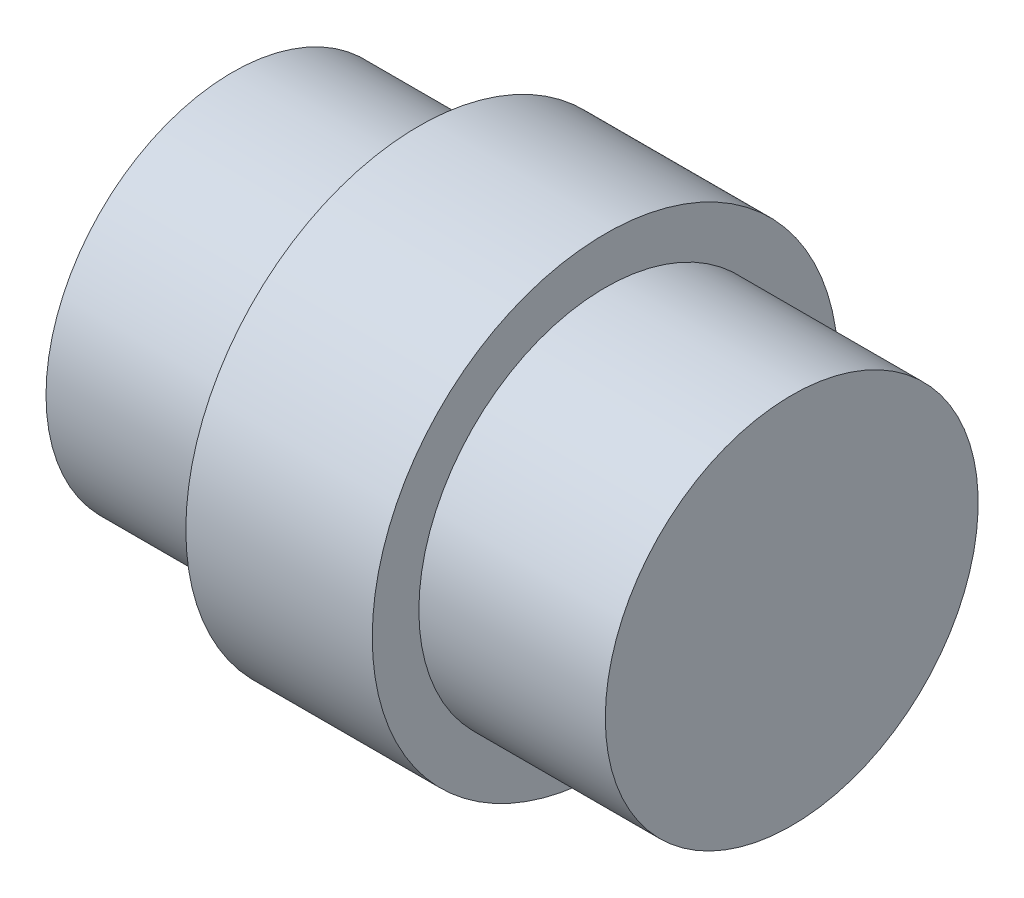
SolidWorks part; units mm, degrees
material "Plain Carbon Steel"
ref_plane "Front Plane" through (0, 0, 0) normal (0, 0, 1) x (1, 0, 0)
ref_plane "Top Plane" through (0, 0, 0) normal (0, 1, 0) x (1, 0, 0)
ref_plane "Right Plane" through (0, 0, 0) normal (1, 0, 0) x (0, 0, -1)
sketch "Sketch1" plane through (0, 0, 0) normal (1, 0, 0) x (0, 0, -1)
  circle A0 centre (0, 0) radius 12.5
  dimension "D1" = 25
extrude "Boss-Extrude1" add sketch "Sketch1" along normal mid plane 30
sketch "Sketch2" plane through (-15, 0, 0) normal (-1, 0, 0) x (0, 0, 1)
  circle A0 centre (0, 0) radius 10
  circle A1 centre (0, 0) radius 12.5
  dimension "D1" = 20
  dimension "D2" = 25
extrude "Cut-Extrude1" cut sketch "Sketch2" against normal blind 10
mirror "Mirror1" about plane through (0, 0, 0) normal (1, 0, 0) of "Cut-Extrude1"
